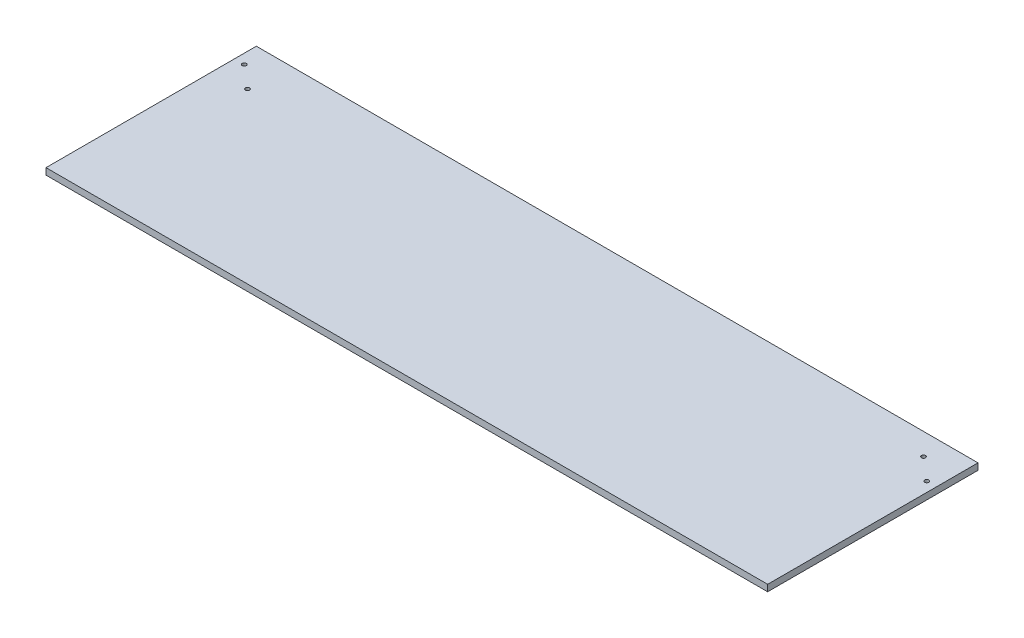
SolidWorks part; units mm, degrees
material "Oak"
ref_plane "Front" through (0, 0, 0) normal (0, 0, 1) x (1, 0, 0)
ref_plane "Top" through (0, 0, 0) normal (0, 1, 0) x (1, 0, 0)
ref_plane "Right" through (0, 0, 0) normal (1, 0, 0) x (0, 0, -1)
sketch "Sketch2" plane through (0, 0, 0) normal (0, 1, 0) x (1, 0, 0)
  line L1 (0, 0) -> (703.33, 0)
  line L2 (0, 0) -> (0, 205)
  line L3 (0, 205) -> (703.33, 205)
  line L4 (703.33, 0) -> (703.33, 205)
  dimension "D1" = 703.33
  dimension "D2" = 205
extrude "Boss-Extrude1" add sketch "Sketch2" along normal blind 6.35
hole_wizard "Ø4.0 (4) Diameter Hole1" positions "Sketch3" profile "Sketch4" hole size "Ø4.0" standard "ANSI Metric"
sketch "Sketch3" plane through (351.6673, 6.35, -173.2428) normal (0, 1, 0) x (-1, 0, 0)
  point P0 (-342.1377, 8.6428)
  point P3 (-319.9127, -10.4072)
  point P6 (319.9127, 8.6428)
  point P9 (342.1377, -10.4072)
sketch "Sketch4" plane through (693.805, 6.35, -164.6) normal (1, 0, 0) x (0, 0, 1)
  line L0 (0, 0) -> (0, 11.2017)
  line L1 (0, 11.2017) -> (2, 10)
  line L2 (2, 10) -> (2, 0)
  line L3 (2, 0) -> (0, 0)
  line L4 (0, 11.2017) -> (-2, 10) construction
  line L5 (0, -6.35) -> (0, 107.95) construction
  dimension "Hole Dia." = 4
  dimension "Hole Depth" = 10
  dimension "Drill Angle" = 118
